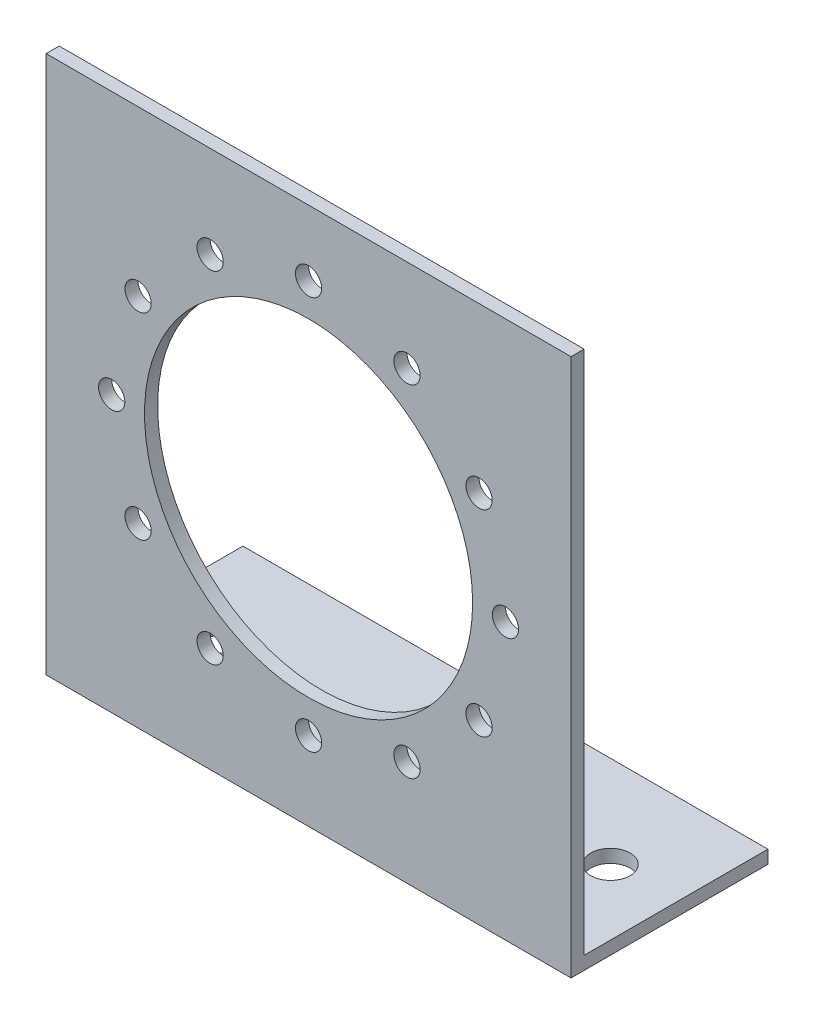
SolidWorks part; units mm, degrees
material "Brass"
ref_plane "Front Plane" through (0, 0, 0) normal (0, 0, 1) x (1, 0, 0)
ref_plane "Top Plane" through (0, 0, 0) normal (0, 1, 0) x (1, 0, 0)
ref_plane "Right Plane" through (0, 0, 0) normal (1, 0, 0) x (0, 0, -1)
sketch "Sketch1" plane through (0, 0, 0) normal (0, 0, 1) x (1, 0, 0)
  line L1 (-20, -20) -> (20, -20)
  line L2 (-20, -20) -> (-20, 20)
  line L3 (-20, 20) -> (20, 20)
  line L4 (20, -20) -> (20, 20)
  line L5 (-20, -20) -> (20, 20) construction
  line L6 (-20, 20) -> (20, -20) construction
  circle A0 centre (0, 0) radius 12.5
  circle A1 centre (0, 15) radius 1
  circle A2 centre (7.5, 12.9904) radius 1
  circle A3 centre (12.9904, 7.5) radius 1
  circle A4 centre (15, 0) radius 1
  circle A5 centre (12.9904, -7.5) radius 1
  circle A6 centre (7.5, -12.9904) radius 1
  circle A7 centre (0, -15) radius 1
  circle A8 centre (-7.5, -12.9904) radius 1
  circle A9 centre (-12.9904, -7.5) radius 1
  circle A10 centre (-15, 0) radius 1
  circle A11 centre (-12.9904, 7.5) radius 1
  circle A12 centre (-7.5, 12.9904) radius 1
  point P0 (0, 0)
  point P34 (0, 0)
  dimension "D3" = 25
  dimension "D4" = 2
  dimension "D1" = 40
  dimension "D2" = 40
  dimension "D5" = 5
  dimension "D6" = 12
extrude "Boss-Extrude2" add sketch "Sketch1" along normal blind 1
sketch "Sketch2" plane through (0, 0, 1) normal (0, 0, 1) x (1, 0, 0)
  line L0 (-20, -20) -> (20, -20) construction
  line L1 (-20, -20) -> (20, -20)
  line L2 (-20, -20) -> (-20, -21)
  line L3 (-20, -21) -> (20, -21)
  line L4 (20, -20) -> (20, -21)
  line L5 (-20, -20) -> (20, -21) construction
  line L6 (-20, -21) -> (20, -20) construction
  point P0 (0, -20.5)
  point P7 (0, -20)
  dimension "D1" = 0.5
  dimension "D2" = 40
  dimension "D3" = 1
extrude "Boss-Extrude3" add sketch "Sketch2" against normal blind 15
sketch "Sketch3" plane through (0, -20, 0) normal (0, 1, 0) x (1, 0, 0)
  line L0 (-20, 14) -> (-20, 0) construction
  line L1 (0, 0) -> (0, 14) construction
  line L2 (20, 14) -> (-20, 14) construction
  circle A0 centre (-15, 7) radius 1.5
  circle A1 centre (15, 7) radius 1.5
  dimension "D1" = 3
  dimension "D2" = 5
extrude "Cut-Extrude1" cut sketch "Sketch3" against normal through all
